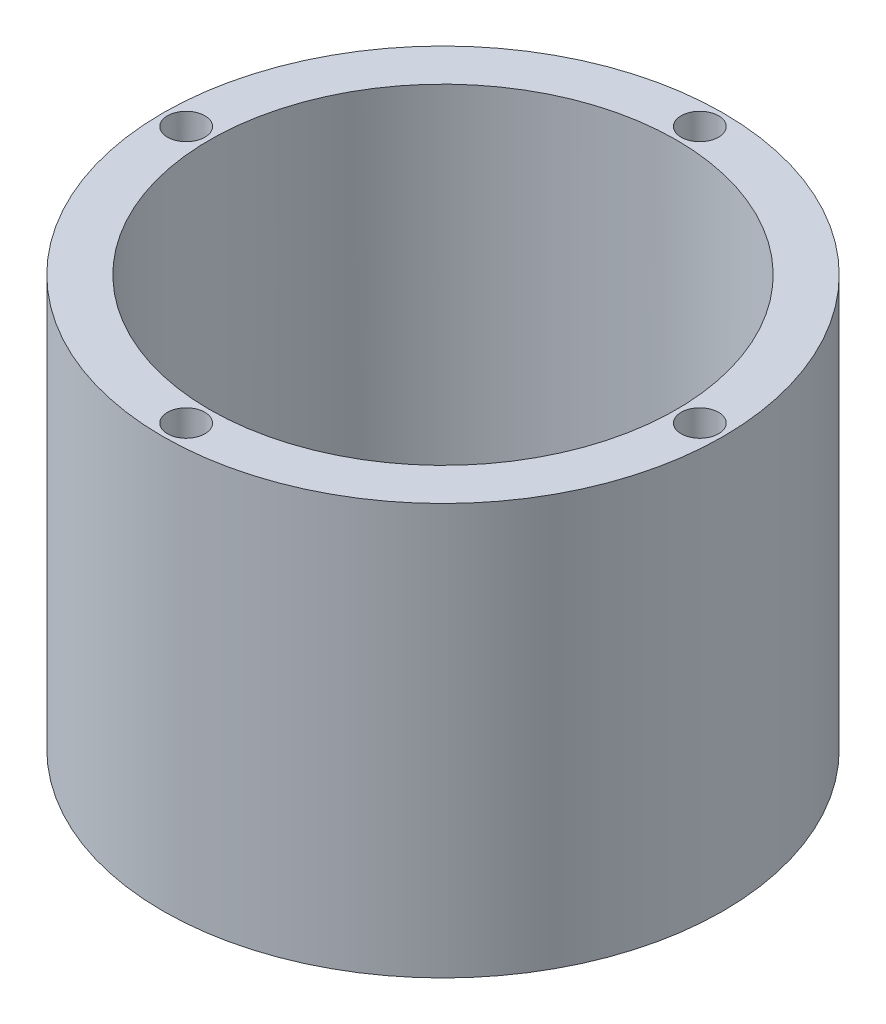
SolidWorks part; units mm, degrees
material "PLA"
ref_plane "Alzado" through (0, 0, 0) normal (0, 0, 1) x (1, 0, 0)
ref_plane "Planta" through (0, 0, 0) normal (0, 1, 0) x (1, 0, 0)
ref_plane "Vista lateral" through (0, 0, 0) normal (1, 0, 0) x (0, 0, -1)
sketch "Croquis1" plane through (0, 0, 0) normal (0, 1, 0) x (1, 0, 0)
  line L0 (0, 0) -> (18, 0) construction
  line L1 (18, -2.1) -> (18, 2.1)
  line L2 (1.9294, 0) -> (1.9294, 3.1786) construction
  line L3 (1.9294, 3.1786) -> (18, 2.1)
  line L4 (0, 0) -> (0, 3.6) construction
  line L5 (1.9294, -3.1786) -> (18, -2.1)
  line L6 (-1.9294, -3.1786) -> (-18, -2.1)
  line L7 (-18, -2.1) -> (-18, 2.1)
  line L8 (-1.9294, 3.1786) -> (-18, 2.1)
  circle A0 centre (0, 0) radius 3.7184 construction
  arc A1 (1.9294, 3.1786) -> (-1.9294, 3.1786) centre (0, 0) ccw
  arc A2 (1.9294, -3.1786) -> (-1.9294, -3.1786) centre (0, 0) cw
sketch "Croquis2" plane through (0, 0, 0) normal (0, 1, 0) x (1, 0, 0)
  circle A0 centre (0, 0) radius 30
extrude "Saliente-Extruir1" add sketch "Croquis2" against normal blind 4
extrude "Cortar-Extruir1" cut sketch "Croquis1" against normal blind 1
sketch "Croquis3" plane through (0, -1, 0) normal (0, 1, 0) x (1, 0, 0)
  circle A0 centre (0, 0) radius 3.7
extrude "Cortar-Extruir2" cut sketch "Croquis3" against normal blind 3
sketch "Croquis5" plane through (0, 0, 0) normal (0, 0, 1) x (1, 0, 0)
  line L0 (0, 80) -> (0, 0) construction
  line L1 (0, 0) -> (30, 0) construction
  line L2 (25, 80) -> (0, 80) construction
  line L4 (30, 0) -> (25, 0)
  line L7 (25, 0) -> (25, 80)
  line L8 (25, 80) -> (30, 80)
  line L9 (30, 80) -> (30, 0)
revolve "Revolución1" add sketch "Croquis5" angle 360 about L0
sketch "Croquis6" plane through (0, 80, 0) normal (0, 1, 0) x (1, 0, 0)
  line L1 (30, 0) -> (25, 0) construction
  circle A0 centre (0, 0) radius 30 construction
  circle A1 centre (0, 0) radius 25 construction
  circle A2 centre (27.5, 0) radius 2
  circle A3 centre (0, -27.5) radius 2
  circle A4 centre (-27.5, 0) radius 2
  circle A5 centre (0, 27.5) radius 2
  point P19 (0, 0)
  dimension "D1" = 4
extrude "Cortar-Extruir3" cut sketch "Croquis6" against normal blind 46
sketch "Croquis7" plane through (0, 0, 0) normal (0, 0, 1) x (1, 0, 0)
  line L0 (0, 0) -> (0, 80) construction
  line L1 (2, 80) -> (-2, 80) construction
  line L2 (30, -4) -> (30, 80) construction
  line L3 (-30, 80) -> (30, 80)
  line L4 (-30, 80) -> (-30, 40)
  line L5 (-30, 40) -> (30, 40)
  line L6 (30, 80) -> (30, 40)
extrude "Cortar-Extruir4" cut sketch "Croquis7" against normal blind 30
mirror "Simetría1" about plane through (0, 0, 0) normal (0, 0, 1) of "Cortar-Extruir4"
